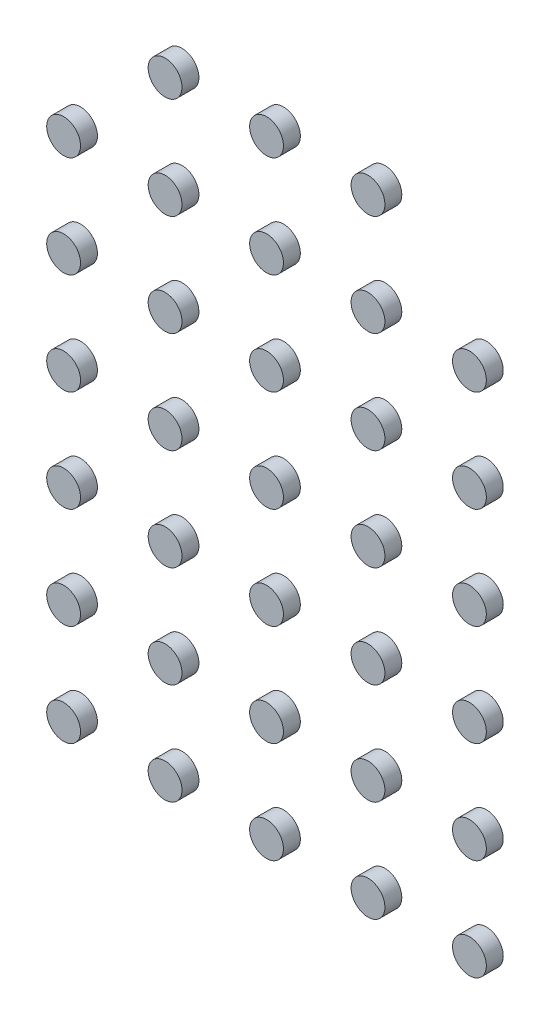
SolidWorks part; units mm, degrees
ref_plane "前视基准面" through (0, 0, 0) normal (0, 0, 1) x (1, 0, 0)
ref_plane "上视基准面" through (0, 0, 0) normal (0, 1, 0) x (1, 0, 0)
ref_plane "右视基准面" through (0, 0, 0) normal (1, 0, 0) x (0, 0, -1)
other "Configuration Table"
sketch "草图1" plane through (0, 0, 0) normal (0, 0, 1) x (1, 0, 0)
  line L0 (-0.7, 0) -> (0.7, 0)
  arc A0 (0.7, 0) -> (-0.7, 0) centre (0, 0) ccw
  dimension "D1" = 1.4
sketch "草图4" plane through (0, 0, 0) normal (0, 0, 1) x (1, 0, 0)
  circle A0 centre (0, 0) radius 0.5
  dimension "D1" = 1
extrude "凸台-拉伸2" add sketch "草图4" along normal blind 0.5
ref_plane "基准面1" through (0, 9, 0) normal (0, 1, 0) x (1, 0, 0)
ref_plane "基准面2" through (6, 0, 0) normal (1, 0, 0) x (0, 0, -1)
delete or keep bodies "实体-删除/保留 1" [suppressed] type delete bodies bodies 265 270 275 280 285 264 269 279 284 263 283 274
sketch "草图5" plane through (0, 0, 0.5) normal (0, 0, 1) x (1, 0, 0)
  circle A1 centre (0, 0) radius 0.5
  circle A2 centre (0, 0) radius 0.5
  dimension "D1" = 0
sketch "草图6" plane through (0, 0, 0) normal (0, 0, 1) x (1, 0, 0)
  circle A1 centre (0, 0) radius 0.5
  circle A2 centre (0, 0) radius 0.5
  dimension "D1" = 0
pattern_linear "阵列(线性)1" count 5 spacing 3 along (1, 0, 0) count 7 spacing 3 along (0, 1, 0) of "凸台-拉伸2"
delete or keep bodies "实体-删除/保留 2" type keep bodies bodies 295 290 309 304 299 294 313 308 303 298 317 293 287 312 307 302 321 297 316 292 311 306 301 296 315 291 310 305 300 318 314 320 322
